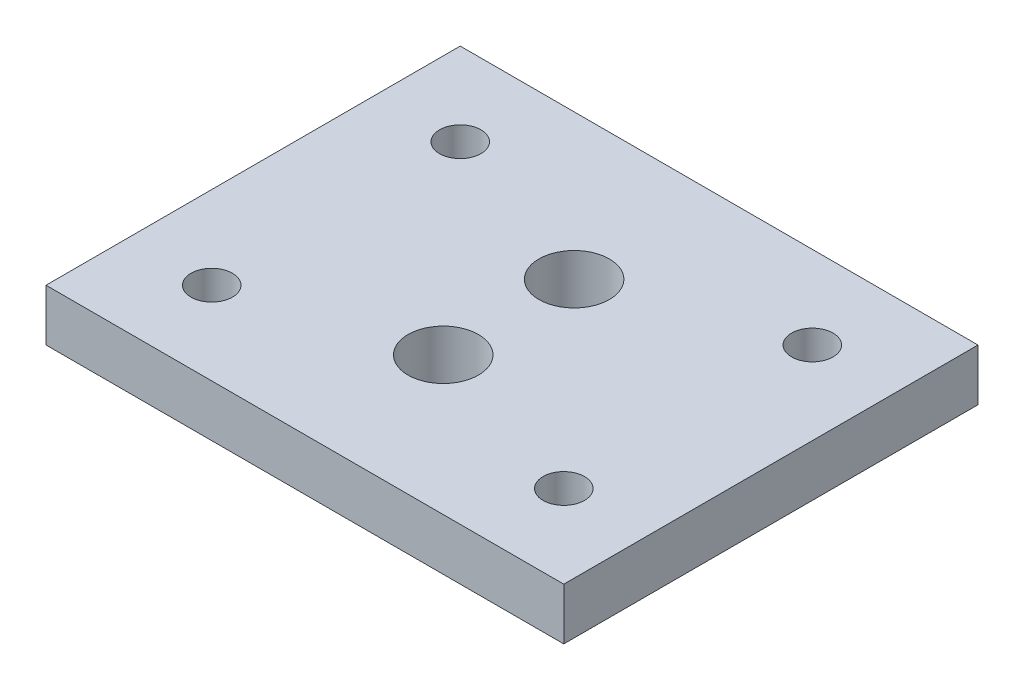
SolidWorks part; units mm, degrees
ref_plane "Front Plane" through (0, 0, 0) normal (1, 0, 0) x (0, 1, 0)
ref_plane "Top Plane" through (0, 0, 0) normal (0, 0, 1) x (0, 1, 0)
ref_plane "Right Plane" through (0, 0, 0) normal (0, 1, 0) x (-1, 0, 0)
ref_plane "Plane1"
sketch "Sketch1" plane through (0, 0, 0) normal (0, 1, 0) x (-1, 0, 0)
  line L0 (0, -25.4) -> (31.75, -25.4)
  line L1 (31.75, -25.4) -> (31.75, 0)
  line L2 (31.75, 0) -> (0, 0)
  line L3 (0, 0) -> (0, -25.4)
  circle A0 centre (5.08, -5.08) radius 1.27
  circle A1 centre (5.08, -20.32) radius 1.27
  circle A2 centre (26.67, -20.32) radius 1.27
  circle A3 centre (26.67, -5.08) radius 1.27
  dimension "D3" = 2.54
  dimension "D4" = 2.54
  dimension "D5" = 2.54
  dimension "D6" = 2.54
  dimension "D1" = 31.75
  dimension "D2" = 25.4
  dimension "D7" = 15.24
  dimension "D8" = 21.59
  dimension "D9" = 21.59
  dimension "D10" = 21.59
  dimension "D11" = 15.24
  dimension "D12" = 15.24
extrude "Extrusion1" add sketch "Sketch1" along normal blind 3.175 contours L2 L3 L0 L1 A3 A2 A1 A0
sketch "Sketch2" plane through (0, 3.175, 0) normal (0, 1, 0) x (-1, 0, 0)
  circle A0 centre (15.875, -8.4836) radius 2.159
  circle A1 centre (15.875, -16.51) radius 2.159
extrude "Extrusion2" cut sketch "Sketch2" against normal through all
